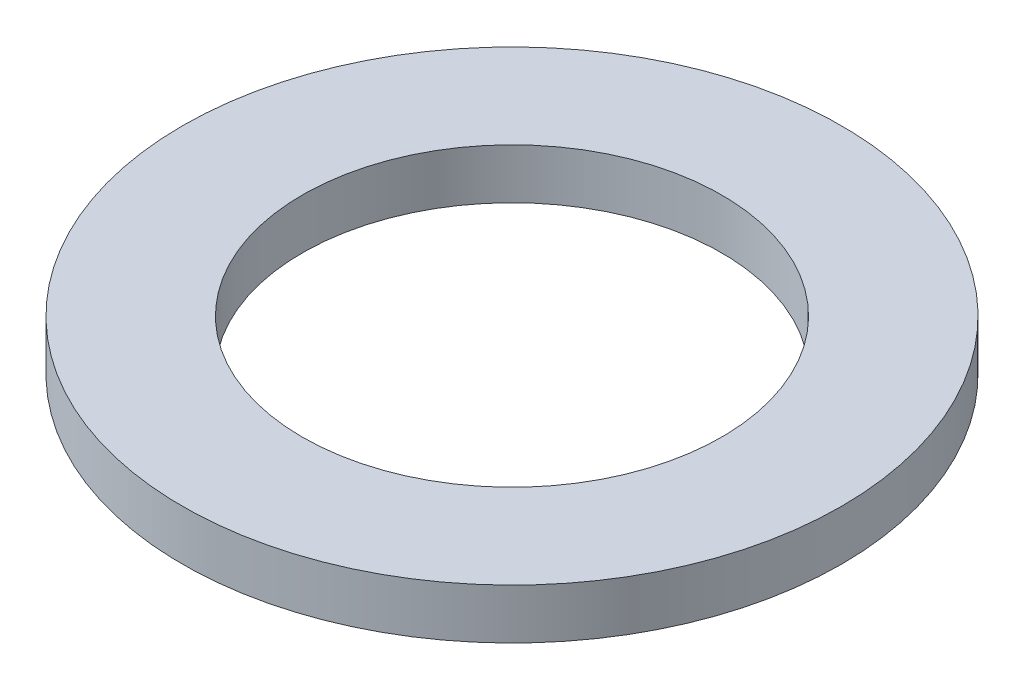
SolidWorks part; units mm, degrees
ref_plane "Front Plane" through (0, 0, 0) normal (0, 0, 1) x (1, 0, 0)
ref_plane "Top Plane" through (0, 0, 0) normal (0, 1, 0) x (1, 0, 0)
ref_plane "Right Plane" through (0, 0, 0) normal (1, 0, 0) x (0, 0, -1)
sketch "Sketch1" plane through (0, 0, 0) normal (0, 1, 0) x (1, 0, 0)
  circle A0 centre (0, 0) radius 14
  dimension "D1" = 28
extrude "Extrude-Thin1" add sketch "Sketch1" along normal blind 3.35 thin
